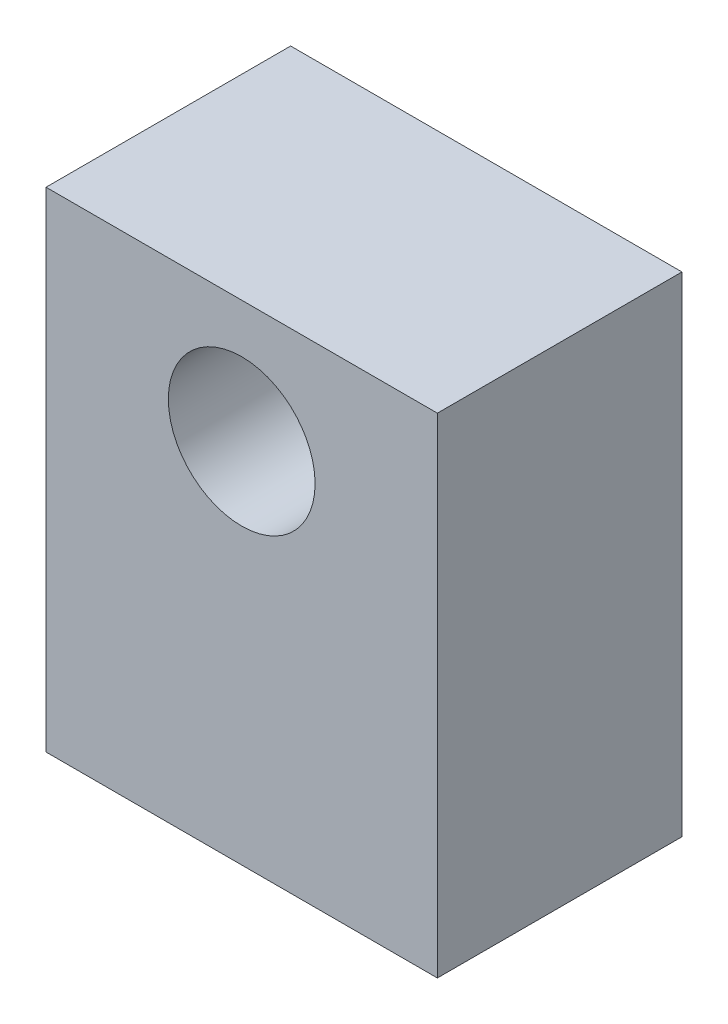
SolidWorks part; units mm, degrees
ref_plane "Plan de face" through (0, 0, 0) normal (0, 0, 1) x (1, 0, 0)
ref_plane "Plan de dessus" through (0, 0, 0) normal (0, 1, 0) x (1, 0, 0)
ref_plane "Plan de droite" through (0, 0, 0) normal (1, 0, 0) x (0, 0, -1)
sketch "Esquisse1" plane through (0, 0, 0) normal (0, 0, 1) x (1, 0, 0)
  line L1 (-4, 5) -> (4, 5)
  line L2 (-4, 5) -> (-4, -5)
  line L3 (-4, -5) -> (4, -5)
  line L4 (4, 5) -> (4, -5)
  line L5 (-4, 5) -> (4, -5) construction
  line L6 (-4, -5) -> (4, 5) construction
  circle A0 centre (0, 2.5) radius 1.5
  point P0 (0, 0)
  point P8 (0, 0)
  dimension "D3" = 3
  dimension "D1" = 8
  dimension "D2" = 10
  dimension "D4" = 2.5
extrude "Boss.-Extru.1" add sketch "Esquisse1" along normal blind 5
